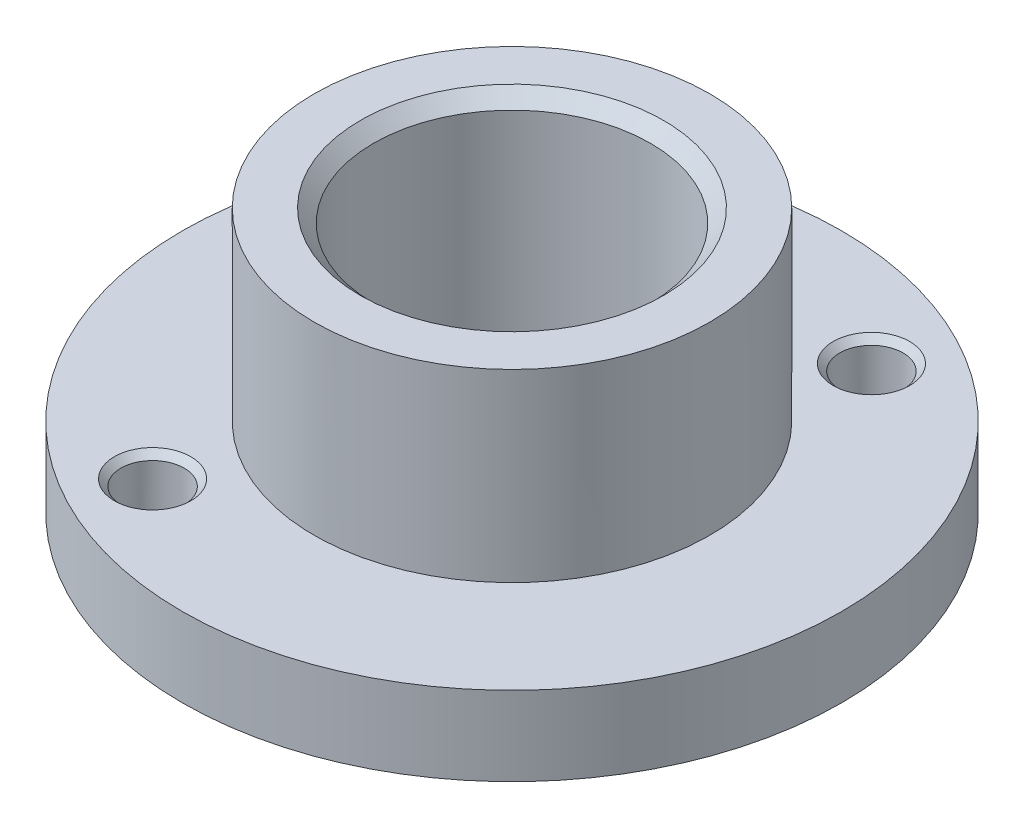
SolidWorks part; units mm, degrees
ref_plane "前视基准面" through (0, 0, 0) normal (0, 0, 1) x (1, 0, 0)
ref_plane "上视基准面" through (0, 0, 0) normal (0, 1, 0) x (1, 0, 0)
ref_plane "右视基准面" through (0, 0, 0) normal (1, 0, 0) x (0, 0, -1)
sketch "草图1" plane through (0, 0, 0) normal (0, 1, 0) x (1, 0, 0)
  circle A0 centre (0, 0) radius 5.25
  circle A1 centre (0, 0) radius 7.5
  dimension "D1" = 15
  dimension "D2" = 10.5
extrude "凸台-拉伸1" add sketch "草图1" along normal blind 10
sketch "草图2" plane through (0, 0, 0) normal (0, -1, 0) x (1, 0, 0)
  circle A0 centre (0, 0) radius 12.5
  circle A1 centre (0, 0) radius 7.5 construction
  circle A2 centre (0, 0) radius 7.5
  dimension "D1" = 25
extrude "凸台-拉伸2" add sketch "草图2" against normal blind 3
hole_wizard "M2 间隙孔1" positions "草图3" profile "草图4" hole size "M2" standard "GB" end condition through all
sketch "草图3" plane through (-33.9487, 3, -19.196) normal (0, 1, 0) x (-0.4922, 0, 0.8705)
  point P0 (-10, 39)
  point P1 (10, 39)
  point P2 (0, 29)
sketch "草图4" plane through (4.9221, 3, -8.7048) normal (1, 0, 0) x (0, 0, 1)
  line L0 (0, 0) -> (0, 3)
  line L1 (0, 3) -> (1.2, 3)
  line L2 (1.2, 3) -> (1.2, 0)
  line L3 (1.2, 0) -> (0, 0)
  line L4 (0, -6.35) -> (0, 107.95) construction
  dimension "通孔孔直径" = 2.4
  dimension "通孔孔深度" = 3
chamfer "倒角1" distance 0.5 angle 45 1 edges at (0, 10, 5.25)
chamfer "倒角2" distance 0.25 angle 45 3 edges at (4.9221, 3, -7.5048) (-4.9221, 3, 9.9048) (-8.7048, 3, -3.7221)
